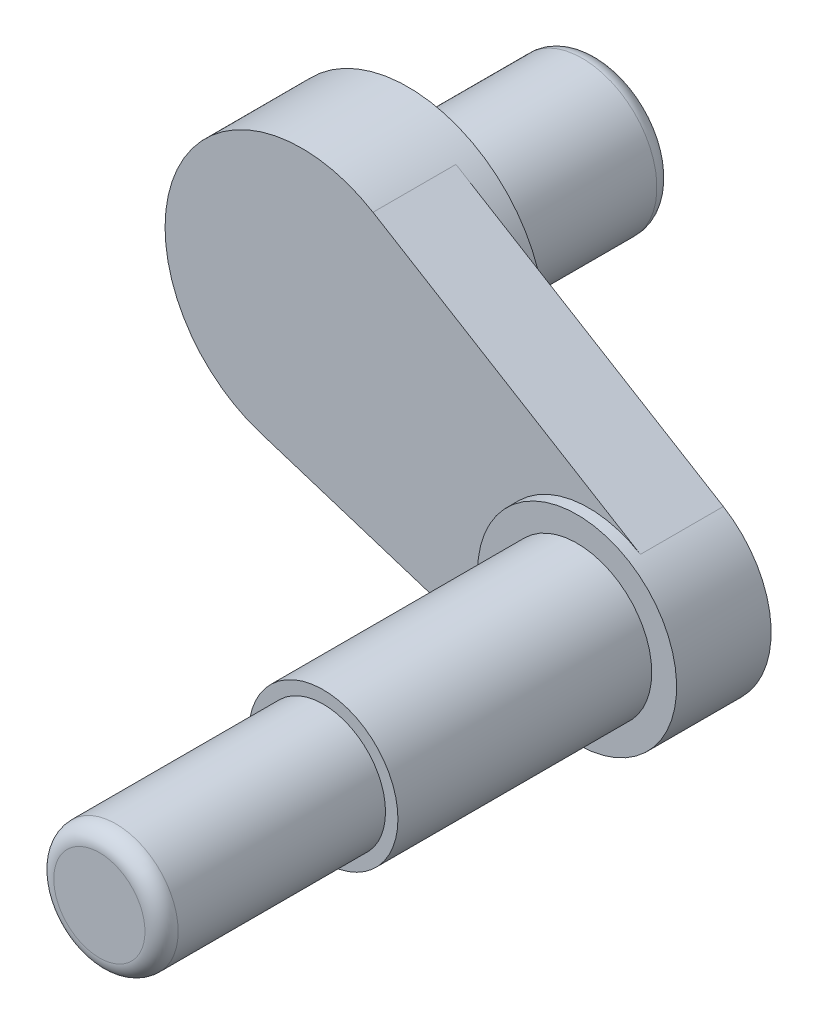
SolidWorks part; units mm, degrees
ref_plane "Ön Düzlem" through (0, 0, 0) normal (0, 0, 1) x (1, 0, 0)
ref_plane "Üst Düzlem" through (0, 0, 0) normal (0, 1, 0) x (1, 0, 0)
ref_plane "Sağ Düzlem" through (0, 0, 0) normal (1, 0, 0) x (0, 0, -1)
sketch "Çizim1" plane through (0, 0, 0) normal (1, 0, 0) x (0, 0, -1)
  line L0 (100, 0) -> (-79, 0) construction
  line L1 (0, 0) -> (0, 45)
  line L2 (0, 45) -> (90, 45)
  line L3 (100, 35) -> (100, 0)
  line L4 (0, 45) -> (0, 50)
  line L5 (0, 50) -> (-15, 50)
  line L6 (-15, 50) -> (-15, 82.5)
  line L7 (-15, 82.5) -> (-79, 82.5)
  line L8 (-79, 82.5) -> (-79, 0)
  line L9 (-15, 50) -> (-15, 0)
  arc A0 (100, 35) -> (90, 45) centre (90, 35) ccw
  dimension "D3" = 10
  dimension "D1" = 100
  dimension "D2" = 45
  dimension "D4" = 5
  dimension "D5" = 15
  dimension "D6" = 32.5
  dimension "D7" = 64
revolve "Döndür1" add sketch "Çizim1" angle 360 about L0
sketch "Çizim2" plane through (0, 0, 79) normal (0, 0, 1) x (1, 0, 0)
  line L0 (0, 0) -> (172.8926, -78.7917) construction
  line L1 (0, 0) -> (0, -48.9285) construction
  line L2 (204.0647, -27.5247) -> (42.8615, 70.4921)
  line L3 (154.6516, -135.9517) -> (-25.0814, -78.595)
  line L4 (42.8615, 70.4921) -> (-25.0814, -78.595)
  arc A0 (154.6516, -135.9517) -> (204.0647, -27.5247) centre (172.8926, -78.7917) ccw
  circle A1 centre (0, 0) radius 82.5 construction
  dimension "D3" = 120
  dimension "D1" = 190
  dimension "D2" = 65.5
extrude "Yükseklik-Ekstrüzyon1" add sketch "Çizim2" against normal blind 50
sketch "Çizim4" plane through (0, 0, 29) normal (0, 0, -1) x (-1, 0, 0)
  circle A0 centre (-172.8926, -78.7917) radius 60
extrude "Yükseklik-Ekstrüzyon2" add sketch "Çizim4" against normal blind 57
sketch "Çizim5" plane through (0, 0, 86) normal (0, 0, 1) x (1, 0, 0)
  circle A0 centre (172.8926, -78.7917) radius 45
  dimension "D1" = 90
extrude "Yükseklik-Ekstrüzyon3" add sketch "Çizim5" along normal blind 153
sketch "Çizim6" plane through (0, 0, 239) normal (0, 0, 1) x (1, 0, 0)
  circle A0 centre (172.8926, -78.7917) radius 37.5
  dimension "D1" = 75
extrude "Yükseklik-Ekstrüzyon4" add sketch "Çizim6" along normal blind 135
fillet "Radyus1" radius 10 1 edges at (210.3926, -78.7917, 374)
